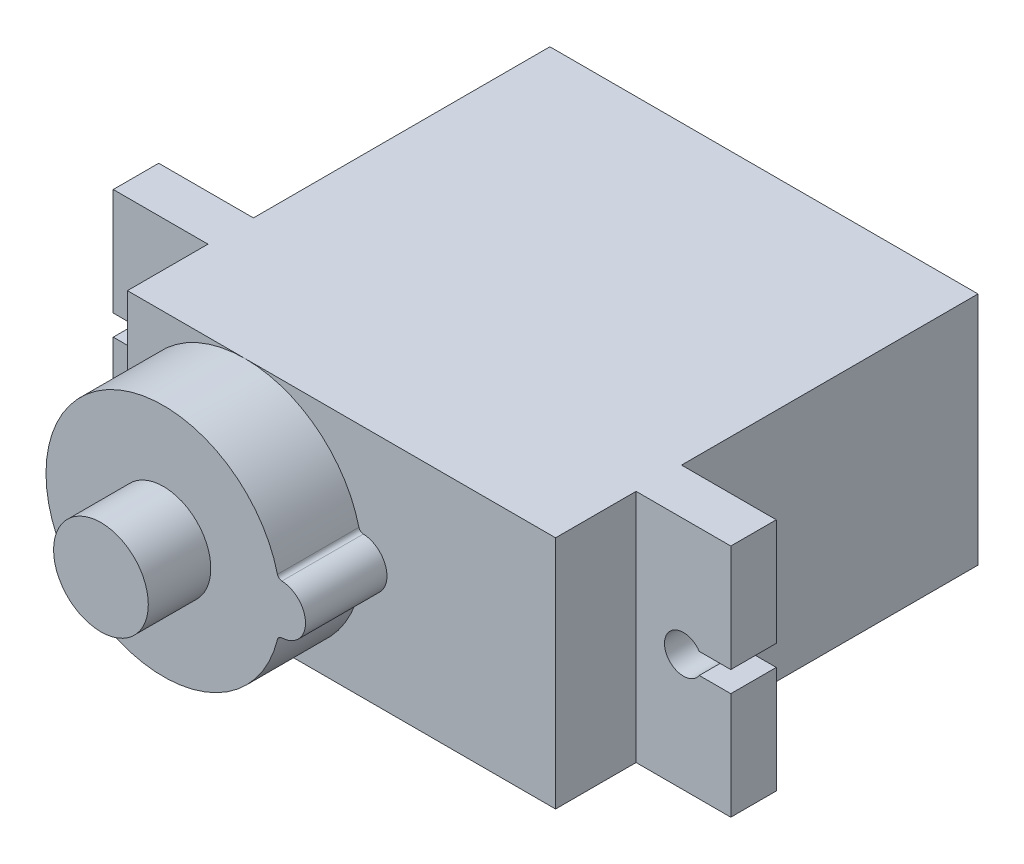
SolidWorks part; units mm, degrees
material "Cast Alloy Steel"
ref_plane "Front Plane" through (0, 0, 0) normal (0, 0, 1) x (1, 0, 0)
ref_plane "Top Plane" through (0, 0, 0) normal (0, 1, 0) x (1, 0, 0)
ref_plane "Right Plane" through (0, 0, 0) normal (1, 0, 0) x (0, 0, -1)
sketch "Sketch1" plane through (0, 0, 0) normal (0, 0, 1) x (1, 0, 0)
  line L1 (-11.3, 6.2) -> (11.3, 6.2)
  line L2 (-11.3, 6.2) -> (-11.3, -6.2)
  line L3 (-11.3, -6.2) -> (11.3, -6.2)
  line L4 (11.3, 6.2) -> (11.3, -6.2)
  line L5 (-11.3, 6.2) -> (11.3, -6.2) construction
  line L6 (-11.3, -6.2) -> (11.3, 6.2) construction
  point P0 (0, 0)
  dimension "D1" = 22.6
  dimension "D2" = 12.4
extrude "Boss-Extrude1" add sketch "Sketch1" along normal blind 22.3
sketch "Sketch2" plane through (0, -6.2, 0) normal (0, -1, 0) x (1, 0, 0)
  line L0 (11.3, 22.3) -> (11.3, 0) construction
  line L1 (11.3, 18.05) -> (16.3, 18.05)
  line L2 (11.3, 18.05) -> (11.3, 15.65)
  line L3 (11.3, 15.65) -> (16.3, 15.65)
  line L4 (16.3, 18.05) -> (16.3, 15.65)
  line L5 (-11.3, 22.3) -> (11.3, 22.3) construction
  line L6 (0, 22.3) -> (0, 0) construction
  line L7 (-16.3, 18.05) -> (-16.3, 15.65)
  line L8 (-11.3, 15.65) -> (-16.3, 15.65)
  line L9 (-11.3, 18.05) -> (-11.3, 15.65)
  line L10 (-11.3, 18.05) -> (-16.3, 18.05)
  dimension "D1" = 5
  dimension "D2" = 2.4
  dimension "D3" = 4.25
extrude "Boss-Extrude2" add sketch "Sketch2" against normal up to vertex (12.4 mm away) up to point (-11.3, 6.2, 22.3)
sketch "Sketch3" plane through (0, 0, 18.05) normal (0, 0, 1) x (1, 0, 0)
  line L0 (14.6352, 0.55) -> (16.3, 0.55)
  line L1 (16.3, 6.2) -> (16.3, -6.2) construction
  line L2 (16.3, 0.55) -> (16.3, -0.55)
  line L3 (16.3, -0.55) -> (14.6352, -0.55)
  line L4 (0, 0) -> (16.3, 0) construction
  line L5 (0, -6.2) -> (0, 6.2) construction
  line L6 (-11.3, -6.2) -> (11.3, -6.2) construction
  line L7 (11.3, 6.2) -> (-11.3, 6.2) construction
  line L8 (-16.3, -0.55) -> (-14.6352, -0.55)
  line L9 (-16.3, 0.55) -> (-16.3, -0.55)
  line L10 (-14.6352, 0.55) -> (-16.3, 0.55)
  arc A0 (14.6352, 0.55) -> (14.6352, -0.55) centre (13.8, 0) ccw
  arc A1 (-14.6352, 0.55) -> (-14.6352, -0.55) centre (-13.8, 0) cw
  point P6 (16.3, 0)
  dimension "D1" = 2
  dimension "D2" = 2.5
  dimension "D3" = 1.1
extrude "Cut-Extrude1" cut sketch "Sketch3" against normal blind 22.3
sketch "Sketch4" plane through (0, 0, 22.3) normal (0, 0, 1) x (1, 0, 0)
  line L0 (-11.3, 6.2) -> (-11.3, -6.2) construction
  arc A4 (0.9186, 1.4888) -> (0.9186, -1.4888) centre (-5.1, 0) ccw
  arc A5 (1.1514, -1.299) -> (1.1514, 1.299) centre (1.1, 0) ccw
  arc A6 (0.9186, -1.4888) -> (1.1514, -1.299) centre (1.1613, -1.5488) cw
  arc A7 (1.1514, 1.299) -> (0.9186, 1.4888) centre (1.1613, 1.5488) cw
  dimension "D1" = 12.4
  dimension "D2" = 2.6
  dimension "D3" = 0.25
extrude "Boss-Extrude3" add sketch "Sketch4" along normal blind 4.3
sketch "Sketch6" plane through (0, 0, 26.6) normal (0, 0, 1) x (1, 0, 0)
  circle A0 centre (-5.1, 0) radius 2.5
  arc A1 (0.9186, 1.4888) -> (0.9186, -1.4888) centre (-5.1, 0) ccw construction
  dimension "D1" = 5
extrude "Boss-Extrude4" add sketch "Sketch6" along normal blind 3.3
sketch "Sketch7" plane through (-11.3, 0, 0) normal (-1, 0, 0) x (0, 0, 1)
  circle A0 centre (4.5, 1.2) radius 0.6
  circle A1 centre (4.5, 0) radius 0.6
  circle A2 centre (4.5, -1.2) radius 0.6
  dimension "D1" = 1.2
  dimension "D2" = 4.5
extrude "Boss-Extrude5" add sketch "Sketch7" along normal blind 3.3 separate body contours A0 | A1 | A2
